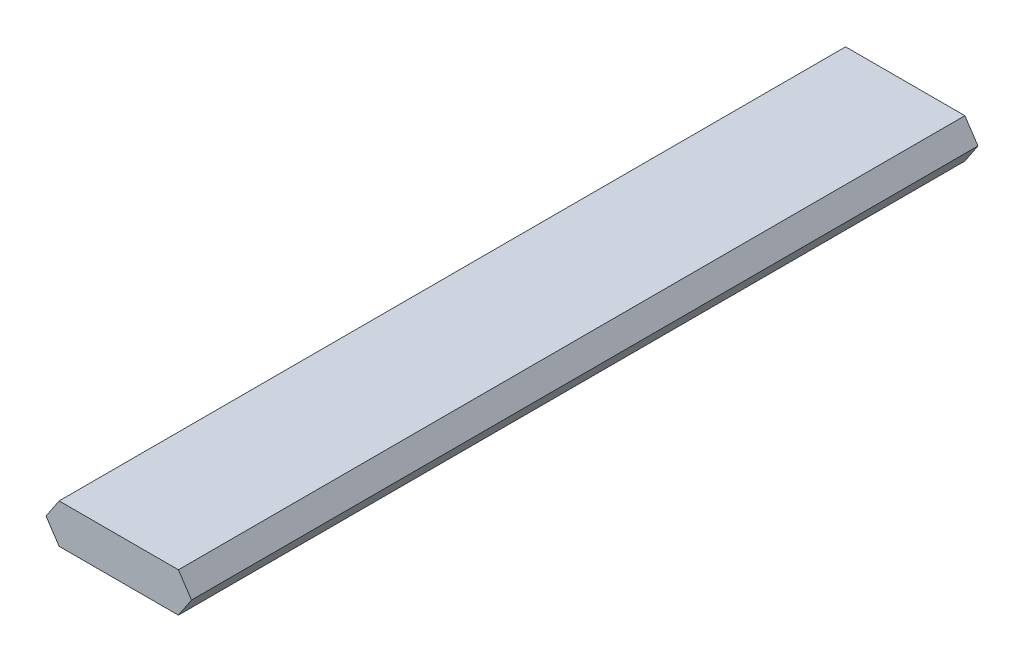
SolidWorks part; units mm, degrees
ref_plane "Plan de face" through (0, 0, 0) normal (0, 0, 1) x (1, 0, 0)
ref_plane "Plan de dessus" through (0, 0, 0) normal (0, 1, 0) x (1, 0, 0)
ref_plane "Plan de droite" through (0, 0, 0) normal (1, 0, 0) x (0, 0, -1)
sketch "Esquisse1" plane through (0, 0, 0) normal (0, 0, 1) x (1, 0, 0)
  line L0 (0, 0) -> (22.2, 0) construction
  line L1 (11.1, 0) -> (11.1, 2.6134) construction
  line L2 (0, 0) -> (2, 3) construction
  line L3 (0, 0) -> (2, 3)
  line L4 (0, 0) -> (2, -3)
  line L5 (22.2, 0) -> (20.2, -3)
  line L6 (22.2, 0) -> (20.2, 3)
  line L7 (2, 3) -> (20.2, 3)
  line L8 (2, -3) -> (20.2, -3)
  dimension "D1" = 2
  dimension "D2" = 3
extrude "Boss.-Extru.1" add sketch "Esquisse1" along normal blind 120
